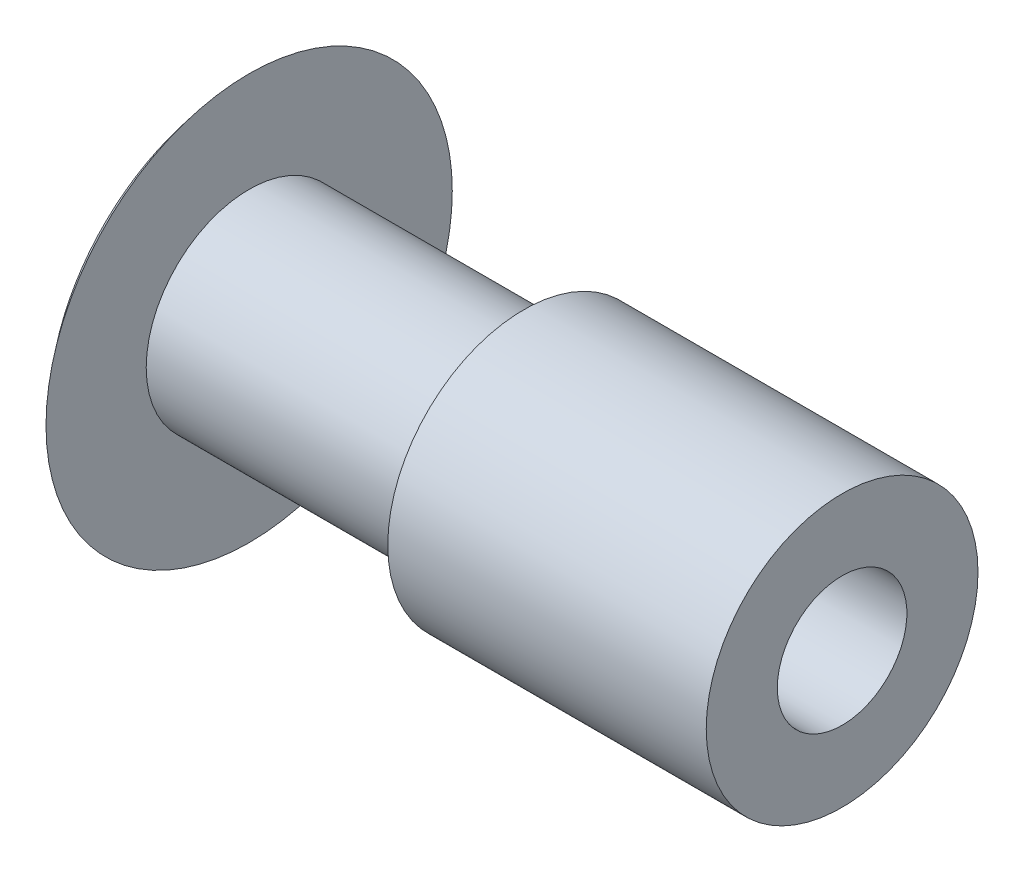
SolidWorks part; units mm, degrees
material "2014 Alloy"
ref_plane "Front Plane" through (0, 0, 0) normal (0, 0, 1) x (1, 0, 0)
ref_plane "Top Plane" through (0, 0, 0) normal (0, 1, 0) x (1, 0, 0)
ref_plane "Right Plane" through (0, 0, 0) normal (1, 0, 0) x (0, 0, -1)
sketch "Sketch1" plane through (0, 0, 0) normal (0, 1, 0) x (1, 0, 0)
  line L0 (0, 0) -> (0, 4.699)
  line L1 (0, 4.699) -> (1.524, 4.699)
  line L2 (1.524, 4.699) -> (1.524, 2.3812)
  line L3 (1.524, 2.3812) -> (7.874, 2.3812)
  line L4 (15.24, 3.1432) -> (15.24, 0)
  line L5 (15.24, 0) -> (0, 0)
  line L6 (7.874, 2.3812) -> (7.874, 3.1432)
  line L7 (7.874, 3.1432) -> (15.24, 3.1432)
  dimension "D1" = 6.35
  dimension "D2" = 13.716
  dimension "D3" = 4.699
  dimension "D4" = 2.3813
  dimension "D5" = 0.762
  dimension "D6" = 1.524
revolve "Revolve1" add sketch "Sketch1" angle 360 about L5
sketch "Sketch2" plane through (0, 0, 0) normal (-1, 0, 0) x (0, 0, 1)
  circle A0 centre (0, 0) radius 1.4986
  dimension "D1" = 2.9972
extrude "Center-Hole" cut sketch "Sketch2" against normal through all
sketch "Sketch3" plane through (0, 0, 0) normal (0, 1, 0) x (1, 0, 0)
  line L0 (1.524, -4.699) -> (1.524, 4.699) construction
  line L1 (0, 4.699) -> (0, -4.699) construction
  line L2 (1.524, 4.699) -> (0, 4.699)
  line L3 (0, 4.699) -> (0, 1.4986)
  line L4 (0, 0) -> (15.24, 0) construction
  line L5 (15.24, -3.1432) -> (15.24, 3.1432) construction
  arc A0 (1.524, 4.699) -> (0, 1.4986) centre (6.6463, 0.2967) ccw
revolve "Cut-Revolve1" cut sketch "Sketch3" angle 360 about L4
